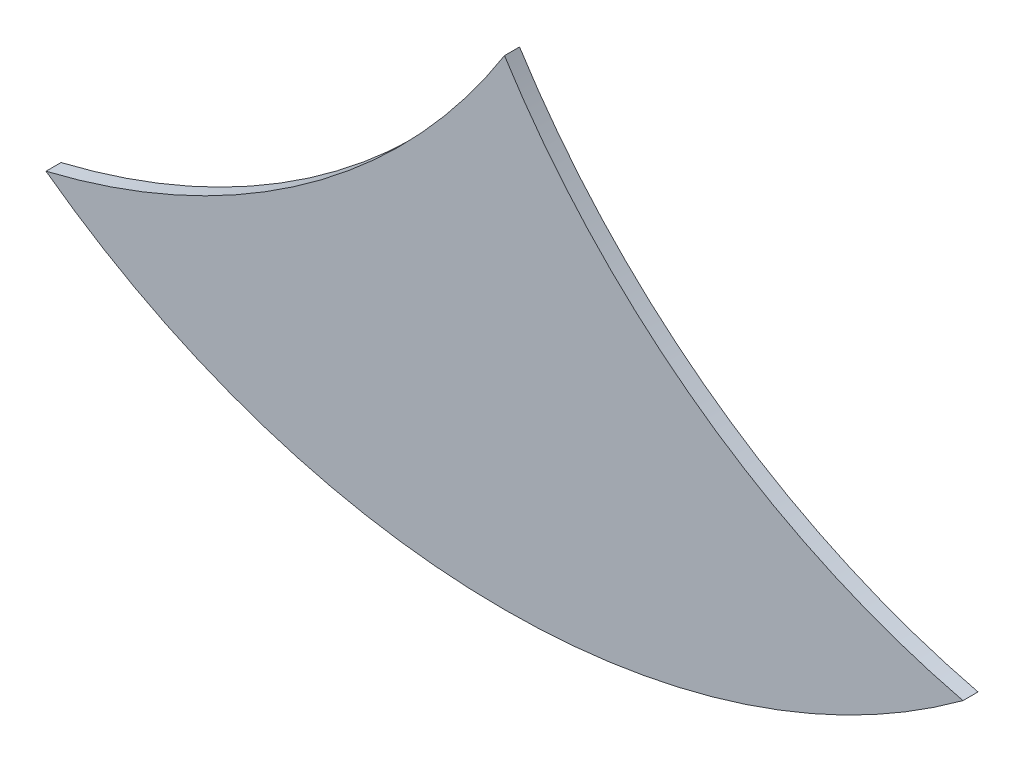
SolidWorks part; units mm, degrees
ref_plane "Alzado" through (0, 0, 0) normal (0, 0, 1) x (1, 0, 0)
ref_plane "Planta" through (0, 0, 0) normal (0, 1, 0) x (1, 0, 0)
ref_plane "Vista lateral" through (0, 0, 0) normal (1, 0, 0) x (0, 0, -1)
sketch "Model" plane through (0, 0, 0) normal (0, 0, 1) x (1, 0, 0)
  arc A0 (31.5287, 18.1136) -> (37.6233, 18.1136) centre (34.576, 22.2554) ccw
  arc A1 (31.5287, 18.1136) -> (34.576, 20.3026) centre (30.3519, 22.9673) ccw
  arc A2 (34.576, 20.3026) -> (37.6233, 18.1136) centre (38.8001, 22.9673) ccw
extrude "Saliente-Extruir1" add sketch "Model" along normal blind 0.1
